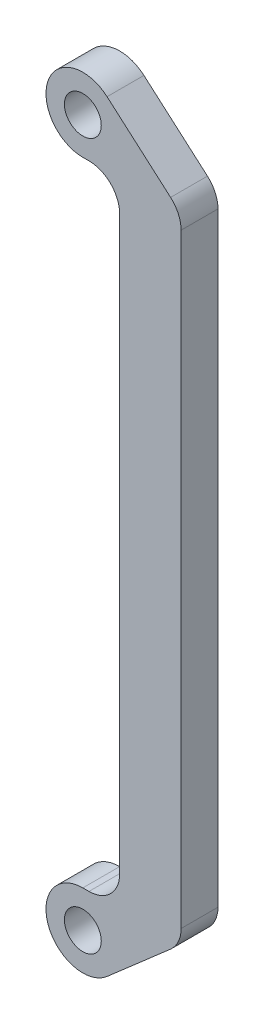
SolidWorks part; units mm, degrees
ref_plane "Alzado" through (0, 0, 0) normal (0, 0, 1) x (1, 0, 0)
ref_plane "Planta" through (0, 0, 0) normal (0, 1, 0) x (1, 0, 0)
ref_plane "Vista lateral" through (0, 0, 0) normal (1, 0, 0) x (0, 0, -1)
sketch "Croquis1" plane through (0, 0, 0) normal (0, 0, 1) x (1, 0, 0)
  line L0 (0, 0) -> (0, 115) construction
  line L2 (0, 121) -> (20.8772, 121) construction
  line L3 (0, -6) -> (20.8772, -6) construction
  line L4 (0, -6) -> (6, -6)
  line L5 (16, -6) -> (6, -6)
  line L6 (16, 8.2727) -> (16, 106.7273)
  line L7 (16, 121) -> (6, 121)
  line L8 (6, 11) -> (6, 104)
  line L9 (0, 6) -> (1, 6)
  line L10 (0, 121) -> (6, 121)
  line L11 (0, 109) -> (1, 109)
  line L12 (14.2877, 110.4944) -> (3.9452, 119.5205)
  line L13 (14.2877, 4.5056) -> (3.9452, -4.5205)
  arc A0 (-6, 0) -> (6, 0) centre (0, 0) ccw
  circle A1 centre (0, 0) radius 3
  circle A3 centre (0, 115) radius 3
  circle A5 centre (0, 0) radius 6
  circle A6 centre (0, 115) radius 6
  arc A7 (6, 104) -> (1, 109) centre (1, 104) ccw
  arc A8 (14.2877, 110.4944) -> (16, 106.7273) centre (11, 106.7273) cw
  arc A9 (16, 8.2727) -> (14.2877, 4.5056) centre (11, 8.2727) cw
  arc A10 (6, 11) -> (1, 6) centre (1, 11) cw
  dimension "D1" = 12
  dimension "D2" = 6
  dimension "D4" = 6
  dimension "D5" = 12
  dimension "D6" = 5
  dimension "D3" = 115
extrude "Saliente-Extruir1" add sketch "Croquis1" along normal blind 6 contours A0 A5 A1 | L8 A10 L9 A5 A0 L13 A9 L6 A8 L12 A6 L11 A7 | A6 A3
